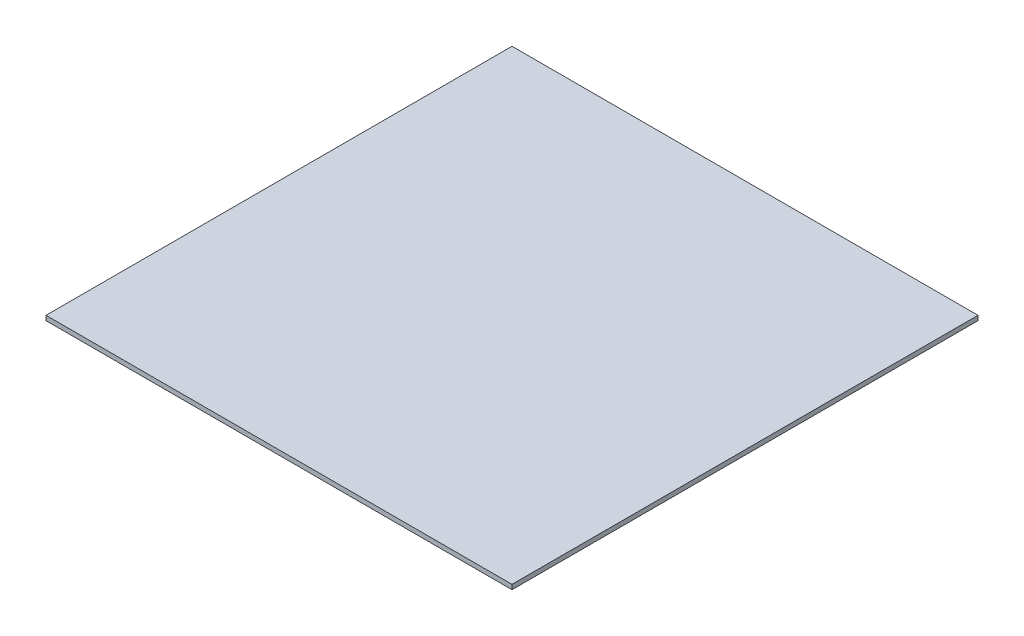
SolidWorks part; units mm, degrees
ref_plane "Front Plane" through (0, 0, 0) normal (0, 0, 1) x (1, 0, 0)
ref_plane "Top Plane" through (0, 0, 0) normal (0, 1, 0) x (1, 0, 0)
ref_plane "Right Plane" through (0, 0, 0) normal (1, 0, 0) x (0, 0, -1)
sketch "Sketch1" plane through (0, 0, 0) normal (0, 1, 0) x (1, 0, 0)
  line L1 (0, 0) -> (-508, 0)
  line L2 (0, 0) -> (0, -508)
  line L3 (0, -508) -> (-508, -508)
  line L4 (-508, 0) -> (-508, -508)
  dimension "D1" = 508
  dimension "D2" = 508
extrude "Boss-Extrude1" add sketch "Sketch1" along normal blind 5.08
